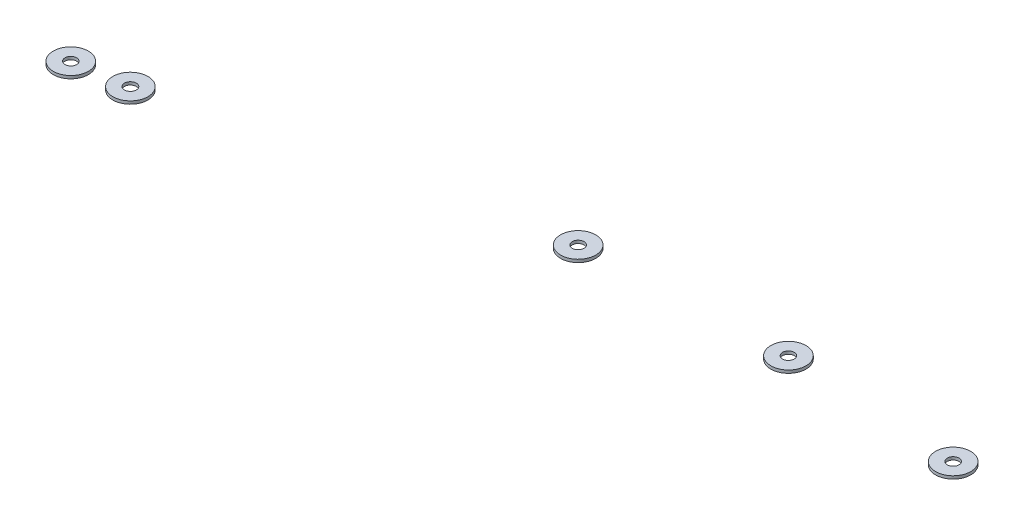
SolidWorks part; units mm, degrees
ref_plane "Płaszczyzna XY" through (0, 0, 0) normal (0, 0, 1) x (1, 0, 0)
ref_plane "Płaszczyzna XZ" through (0, 0, 0) normal (0, 1, 0) x (1, 0, 0)
ref_plane "Płaszczyzna YZ" through (0, 0, 0) normal (1, 0, 0) x (0, 0, -1)
sketch "Szkic1" plane through (0, 705.3, 0) normal (0, 1, 0) x (1, 0, 0)
  circle A0 centre (-94.9095, -263.8022) radius 2
  circle A1 centre (-94.9095, -263.8022) radius 6
  circle A2 centre (-154.3447, -260.6438) radius 2
  circle A3 centre (-154.3447, -260.6438) radius 6
  circle A4 centre (-223.0248, -263.8022) radius 2
  circle A5 centre (-223.0248, -263.8022) radius 6
  circle A6 centre (-346.3728, -293.4293) radius 2.0342
  circle A7 centre (-364.0511, -296.1018) radius 2
  circle A8 centre (-346.3728, -293.4293) radius 6
  circle A9 centre (-364.0511, -296.1018) radius 6
  dimension "D1" = 12
  dimension "D2" = 12
  dimension "D3" = 12
  dimension "D4" = 12
  dimension "D5" = 12
extrude "Dodanie-wyciągnięcie1" add sketch "Szkic1" along normal blind 1
